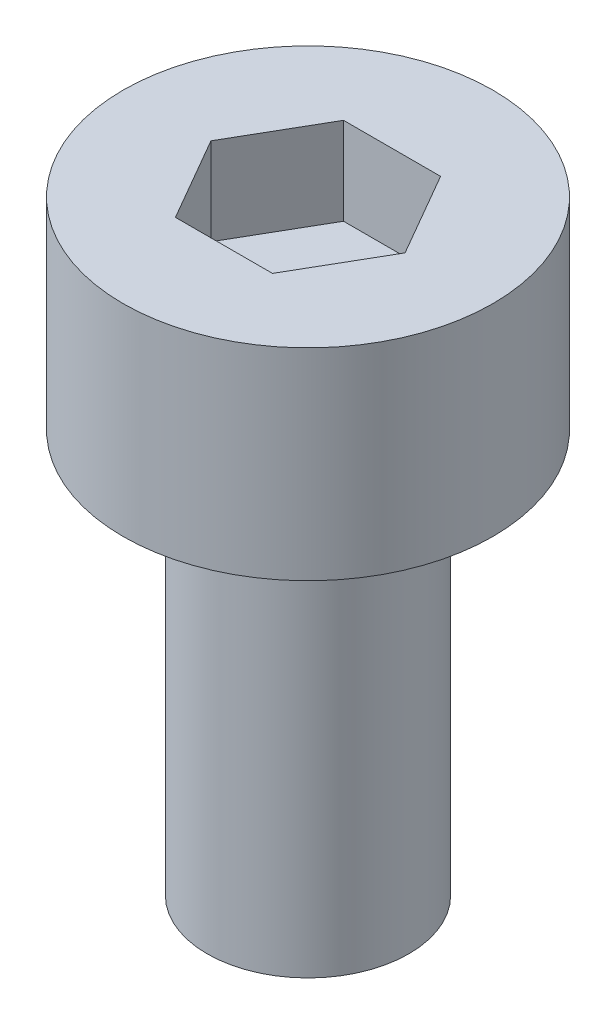
SolidWorks part; units mm, degrees
material "AISI 304"
ref_plane "前视基准面" through (0, 0, 0) normal (0, 0, 1) x (1, 0, 0)
ref_plane "上视基准面" through (0, 0, 0) normal (0, 1, 0) x (1, 0, 0)
ref_plane "右视基准面" through (0, 0, 0) normal (1, 0, 0) x (0, 0, -1)
sketch "草图1" plane through (0, 0, 0) normal (0, 1, 0) x (1, 0, 0)
  circle A0 centre (0, 0) radius 2.75
  dimension "D1" = 5.5
extrude "杯头" add sketch "草图1" along normal blind 3
sketch "草图2" plane through (0, 3, 0) normal (0, 1, 0) x (1, 0, 0)
  line L1 (1.4434, 0) -> (0.7217, 1.25)
  line L2 (0.7217, 1.25) -> (-0.7217, 1.25)
  line L3 (-0.7217, 1.25) -> (-1.4434, 0)
  line L4 (-1.4434, 0) -> (-0.7217, -1.25)
  line L5 (-0.7217, -1.25) -> (0.7217, -1.25)
  line L6 (0.7217, -1.25) -> (1.4434, 0)
  circle A0 centre (0, 0) radius 1.25 construction
  dimension "D1" = 2.5
extrude "内六角口" cut sketch "草图2" against normal blind 1.3
sketch "草图3" plane through (0, 0, 0) normal (0, -1, 0) x (1, 0, 0)
  circle A0 centre (0, 0) radius 1.5
  dimension "D1" = 3
extrude "螺纹长" add sketch "草图3" along normal blind 6
